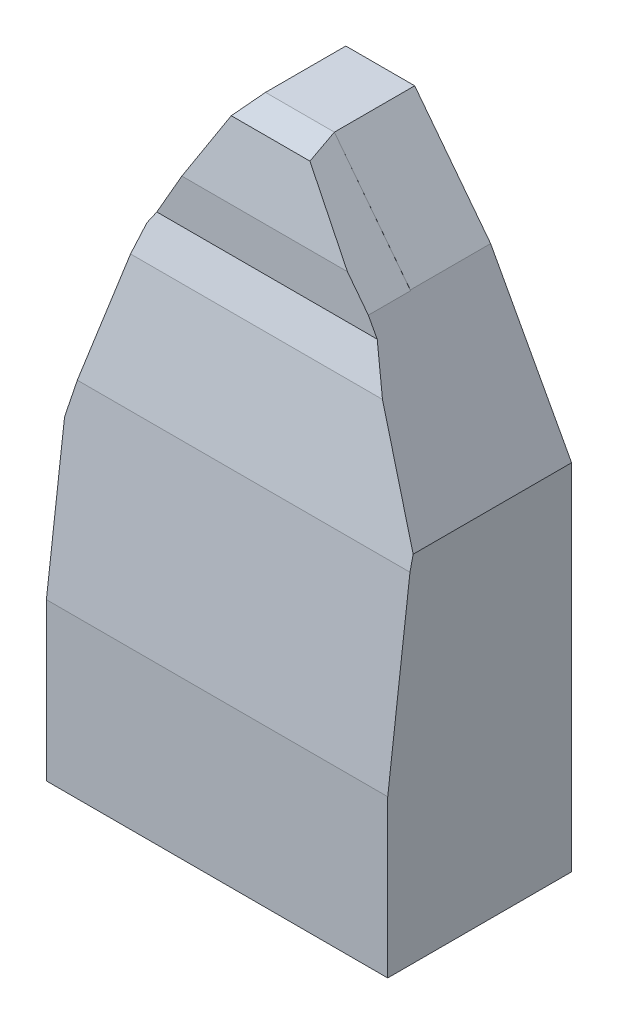
SolidWorks part; units mm, degrees
ref_plane "Front Plane" through (0, 0, 0) normal (0, 0, 1) x (1, 0, 0)
ref_plane "Top Plane" through (0, 0, 0) normal (0, 1, 0) x (1, 0, 0)
ref_plane "Right Plane" through (0, 0, 0) normal (1, 0, 0) x (0, 0, -1)
sketch "Sketch1" plane through (0, 0, 0) normal (0, 0, 1) x (1, 0, 0)
  line L0 (0, 0) -> (431.8, 0)
  line L1 (431.8, 0) -> (431.8, 387.4034)
  line L2 (431.8, 387.4034) -> (377.0655, 602.775)
  line L3 (377.0655, 602.775) -> (285.6418, 762)
  line L4 (285.6418, 762) -> (198.5042, 762)
  line L5 (198.5042, 762) -> (102.4538, 637.1345)
  line L6 (102.4538, 637.1345) -> (0, 448.2353)
  line L7 (0, 448.2353) -> (0, 0)
  dimension "D1" = 762
  dimension "D2" = 431.8
extrude "Boss-Extrude1" add sketch "Sketch1" along normal blind 101.6
sketch "Sketch2" plane through (0, 0, 0) normal (-1, 0, 0) x (0, 0, 1)
  line L0 (101.6, 0) -> (232.6217, 0)
  line L1 (232.6217, 0) -> (232.6217, 198.6482)
  line L2 (232.6217, 198.6482) -> (204.4518, 430.5066)
  line L3 (204.4518, 430.5066) -> (172.7805, 570.8119)
  line L4 (172.7805, 570.8119) -> (155.0893, 615.7047)
  line L5 (155.0893, 615.7047) -> (155.0893, 670.9083)
  line L6 (155.0893, 670.9083) -> (139.6079, 752.7874)
  line L8 (139.6079, 752.7874) -> (101.6, 762)
  line L9 (101.6, 762) -> (101.6, 0)
  dimension "D1" = 0
  dimension "D2" = 0
extrude "Boss-Extrude2" add sketch "Sketch2" against normal up to surface (431.8 mm away) up to face at (431.8, 193.7017, 50.8)
sketch "Sketch3" plane through (0, 0, 101.6) normal (0, 0, -1) x (-1, 0, 0)
  line L0 (0, 448.2353) -> (-102.0796, 636.4445)
  line L1 (0, 448.2353) -> (-102.4538, 637.1345) construction
  line L2 (-102.0796, 636.4445) -> (-205.0523, 770.5126)
  line L3 (-102.4538, 637.1345) -> (-198.5042, 762) construction
  line L4 (-205.0523, 770.5126) -> (-205.0523, 987.3428)
  line L5 (-205.0523, 987.3428) -> (227.8795, 941.9217)
  line L6 (227.8795, 941.9217) -> (179.7159, 482.8494)
  line L7 (179.7159, 482.8494) -> (0, 448.2353)
extrude "Cut-Extrude1" cut sketch "Sketch3" against normal through all
sketch "Sketch4" plane through (0, 0, 101.6) normal (0, 0, -1) x (-1, 0, 0)
  line L0 (-431.8, 387.4034) -> (-377.0655, 602.775)
  line L1 (-377.0655, 602.775) -> (-285.6418, 762)
  line L2 (-285.6418, 762) -> (-386.6478, 961.5261)
  line L3 (-386.6478, 961.5261) -> (-935.091, 961.5261)
  line L4 (-935.091, 961.5261) -> (-884.9139, 472.9491)
  line L5 (-884.9139, 472.9491) -> (-431.8, 387.4034)
extrude "Cut-Extrude2" cut sketch "Sketch4" against normal through all
mirror "Mirror1" about plane through (0, 0, 0) normal (1, 0, 0) of "Cut-Extrude2", "Cut-Extrude1", "Boss-Extrude2", "Boss-Extrude1"
sketch "Sketch5" plane through (0, 0, 0) normal (0, 0, 1) x (1, 0, 0)
  line L1 (0, 0) -> (672.516, 0)
  line L2 (0, 0) -> (0, 895.0699)
  line L3 (0, 895.0699) -> (672.516, 895.0699)
  line L4 (672.516, 0) -> (672.516, 895.0699)
extrude "Cut-Extrude3" cut sketch "Sketch5" along normal through all
